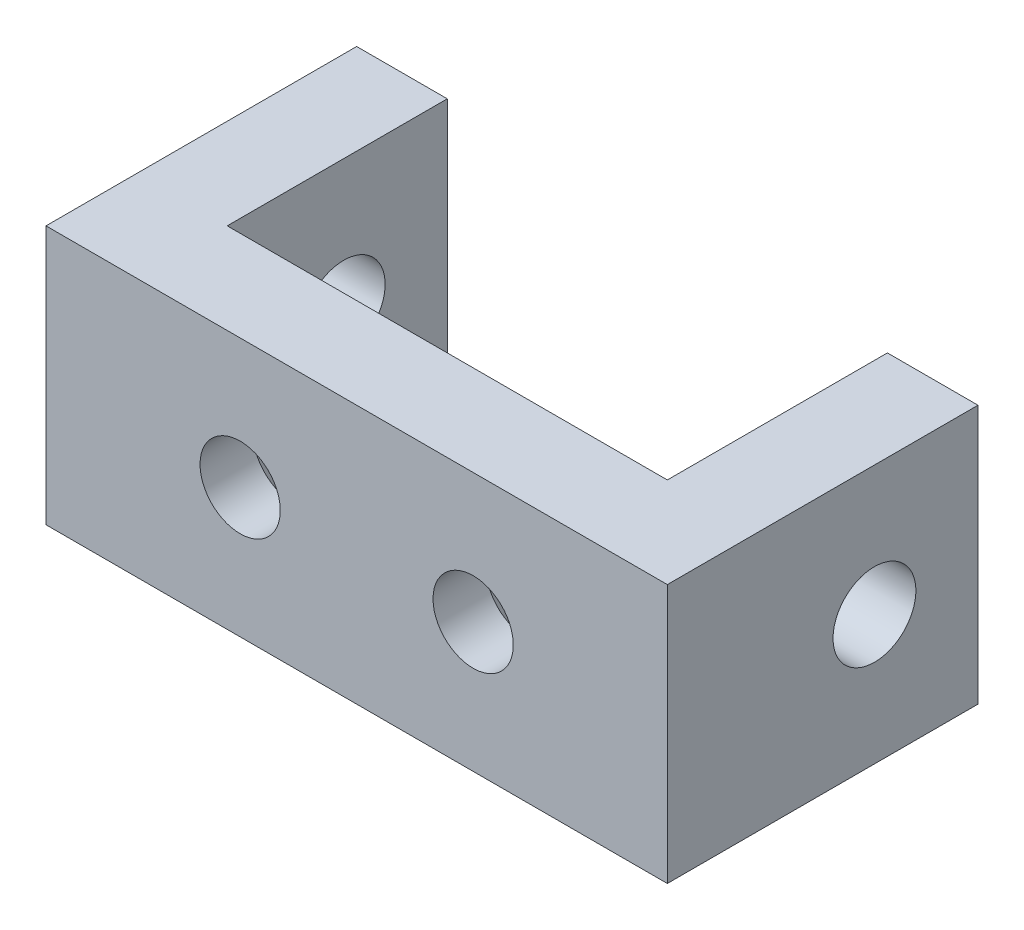
SolidWorks part; units mm, degrees
ref_plane "Front" through (0, 0, 0) normal (0, 0, 1) x (1, 0, 0)
ref_plane "Top" through (0, 0, 0) normal (0, 1, 0) x (1, 0, 0)
ref_plane "Right" through (0, 0, 0) normal (1, 0, 0) x (0, 0, -1)
sketch "Sketch1" plane through (0, 0, 0) normal (0, 1, 0) x (1, 0, 0)
  line L1 (-8.5, -1.75) -> (8.5, -1.75)
  line L2 (-8.5, -1.75) -> (-8.5, 1.75)
  line L3 (-8.5, 1.75) -> (8.5, 1.75)
  line L4 (8.5, -1.75) -> (8.5, 1.75)
  line L5 (-8.5, -1.75) -> (8.5, 1.75) construction
  line L6 (-8.5, 1.75) -> (8.5, -1.75) construction
  line L7 (8.5, -1.75) -> (12, -1.75)
  line L8 (8.5, -1.75) -> (8.5, 10.25)
  line L9 (8.5, 10.25) -> (12, 10.25)
  line L10 (12, -1.75) -> (12, 10.25)
  line L11 (8.5, -1.75) -> (12, 10.25) construction
  line L12 (8.5, 10.25) -> (12, -1.75) construction
  line L13 (-8.5, -1.75) -> (-12, -1.75)
  line L14 (-8.5, -1.75) -> (-8.5, 10.25)
  line L15 (-8.5, 10.25) -> (-12, 10.25)
  line L16 (-12, -1.75) -> (-12, 10.25)
  line L17 (-8.5, -1.75) -> (-12, 10.25) construction
  line L18 (-8.5, 10.25) -> (-12, -1.75) construction
  point P0 (0, 0)
  point P9 (10.25, 4.25)
  point P13 (-10.25, 4.25)
  dimension "D1" = 3.5
  dimension "D2" = 17
  dimension "D3" = 12
  dimension "D4" = 3.5
  dimension "D5" = 12
  dimension "D6" = 3.5
extrude "Boss-Extrude1" add sketch "Sketch1" along normal blind 10 contours L16 L13 L2 L14 L15 | L1 L4 L3 L2 | L7 L10 L9 L8 L4
sketch "Sketch2" plane through (-12, 0, 0) normal (-1, 0, 0) x (0, 0, 1)
  line L0 (-10.25, 5) -> (-6.25, 5) construction
  line L1 (-10.25, 10) -> (-10.25, 0) construction
  circle A0 centre (-6.25, 5) radius 1.6
  dimension "D2" = 3.2
  dimension "D1" = 4
extrude "Cut-Extrude1" cut sketch "Sketch2" against normal through all
sketch "Sketch3" plane through (0, 0, -1.75) normal (0, 0, -1) x (-1, 0, 0)
  line L0 (8.5, 0) -> (-8.5, 0) construction
  circle A0 centre (-4.5, 5) radius 1.5
  circle A1 centre (4.5, 5) radius 1.5
  dimension "D1" = 3
  dimension "D2" = 3
  dimension "D3" = 5
  dimension "D4" = 4.5
  dimension "D5" = 4.5
extrude "Cut-Extrude2" cut sketch "Sketch3" against normal through all
hole_wizard "CSK for M4 Countersunk Flat Head Screw1" positions "3DSketch1" profile "Sketch4" countersink size "M4" standard "ISO" end condition through all
sketch3d "3DSketch1"
  line L0 (4.5, 5, 1.75) -> (4.5, 5, -1.75) construction
  line L1 (-4.5, 5, 1.75) -> (-4.5, 5, -1.75) construction
  point P0 (4.5, 5, -1.75)
  point P4 (-4.5, 5, -1.75)
sketch "Sketch4" plane through (4.5, 5, -1.75) normal (1, 0, 0) x (0, 1, 0)
  line L0 (0, 0) -> (0, 3.5)
  line L1 (0, 3.5) -> (1.55, 3.5)
  line L2 (1.55, 3.5) -> (1.55, 1.45)
  line L3 (1.55, 1.45) -> (3, 0)
  line L5 (3, 0) -> (0, 0)
  line L6 (-1.55, 1.45) -> (-3, 0) construction
  line L11 (0, -6.35) -> (0, 107.95) construction
  dimension "Thru Hole Dia." = 3.1
  dimension "Thru Hole Depth" = 3.5
  dimension "Near C'Sink Dia." = 6
  dimension "Near C'Sink Angle" = 90
